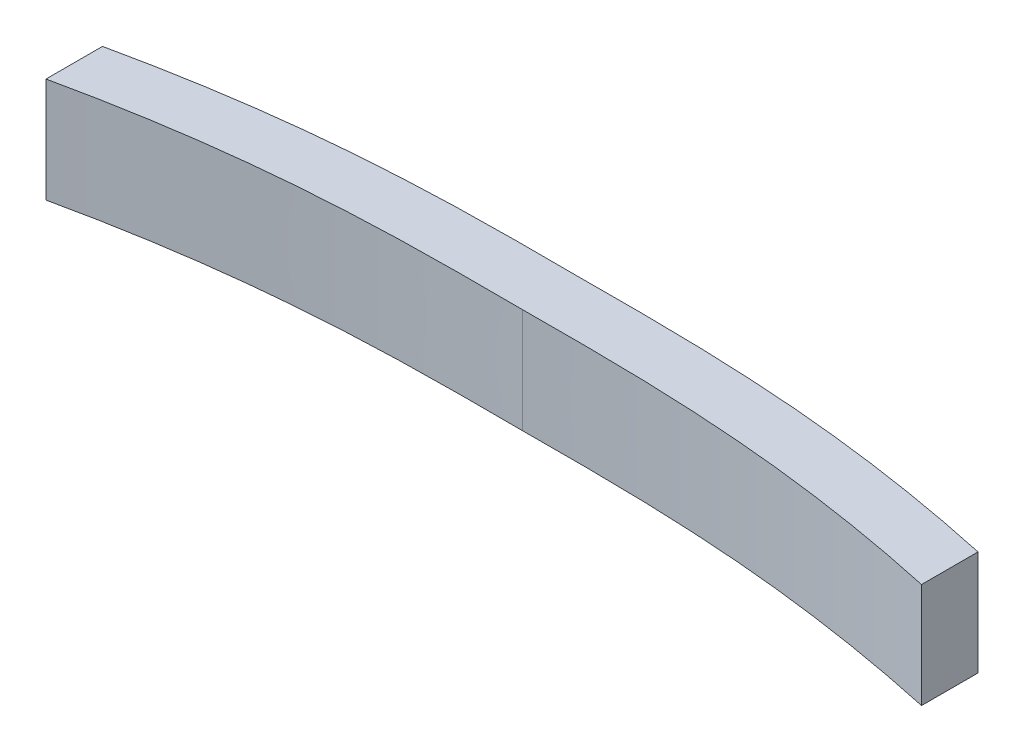
SolidWorks part; units mm, degrees
ref_plane "Front Plane" through (0, 0, 0) normal (0, 0, 1) x (1, 0, 0)
ref_plane "Top Plane" through (0, 0, 0) normal (0, 1, 0) x (1, 0, 0)
ref_plane "Right Plane" through (0, 0, 0) normal (1, 0, 0) x (0, 0, -1)
sketch "Sketch1" plane through (0, 0, 0) normal (0, 1, 0) x (1, 0, 0)
  line L0 (189.6667, 320) -> (948.3333, 320) construction
  line L1 (-903.6669, 221.9416) -> (-806.6741, 223.1267) construction
  line L2 (-2.4415, 6.8053) -> (-2.4415, 30.0052) construction
  line L3 (-115.408, 6.8053) -> (110.5249, 6.8053)
  line L4 (-115.408, 6.8053) -> (-115.408, -50.1579)
  line L5 (-115.408, -50.1579) -> (110.5249, -50.1579)
  line L6 (110.5249, 6.8053) -> (110.5249, -50.1579)
  line L7 (-2.4415, 6.8053) -> (-2.4415, -2.9496) construction
  line L8 (-56.7109, 8.0428) -> (-56.7109, -1.9572)
  line L9 (51.8279, 8.0428) -> (51.8279, -1.9572)
  line L10 (-56.7109, 10.0428) -> (-56.7109, -3.9572)
  line L11 (51.8279, -3.9572) -> (51.8279, 10.0428)
  spline S0 degree 3 poles (-56.7109, 8.0428) (-48.3237, 9.8705) (-35.0274, 11.9379) (-16.8793, 12.8603) (-7.6058, 12.8449) (-2.4415, 12.8177) knots 0 0 0 0 0.472031 0.735861 1 1 1 1
  spline S1 degree 3 poles (-56.7109, -1.9572) (-48.3237, -0.1295) (-35.0274, 1.9379) (-16.8793, 2.8603) (-7.6058, 2.8449) (-2.4415, 2.8177) knots 0 0 0 0 0.472031 0.735861 1 1 1 1
  spline S2 degree 3 poles (51.8279, -1.9572) (43.4407, -0.1295) (30.1443, 1.9379) (11.9963, 2.8603) (2.7228, 2.8449) (-2.4415, 2.8177) knots 0 0 0 0 0.472031 0.735861 1 1 1 1
  spline S3 degree 3 poles (51.8279, 8.0428) (43.4407, 9.8705) (30.1443, 11.9379) (11.9963, 12.8603) (2.7228, 12.8449) (-2.4415, 12.8177) knots 0 0 0 0 0.472031 0.735861 1 1 1 1
  spline S4 degree 3 poles (-56.7109, 10.0428) (-48.3237, 11.8705) (-35.0274, 13.9379) (-16.8793, 14.8603) (-7.6058, 14.8449) (-2.4415, 14.8177) knots 0 0 0 0 0.472031 0.735861 1 1 1 1
  spline S5 degree 3 poles (51.8279, 10.0428) (43.4407, 11.8705) (30.1443, 13.9379) (11.9963, 14.8603) (2.7228, 14.8449) (-2.4415, 14.8177) knots 0 0 0 0 0.472031 0.735861 1 1 1 1
  spline S6 degree 3 poles (-56.7109, -3.9572) (-48.3237, -2.1295) (-35.0274, -0.0621) (-16.8793, 0.8603) (-7.6058, 0.8449) (-2.4415, 0.8177) knots 0 0 0 0 0.472031 0.735861 1 1 1 1
  spline S7 degree 3 poles (51.8279, -3.9572) (43.4407, -2.1295) (30.1443, -0.0621) (11.9963, 0.8603) (2.7228, 0.8449) (-2.4415, 0.8177) knots 0 0 0 0 0.472031 0.735861 1 1 1 1
  spline S8 degree 3 poles (-56.7109, 3.0428) (-48.3237, 4.8705) (-35.0274, 6.9379) (-16.8793, 7.8603) (-7.6058, 7.8449) (-2.4415, 7.8177) knots 0 0 0 0 0.472031 0.735861 1 1 1 1
  spline S9 degree 3 poles (51.8279, 3.0428) (43.4407, 4.8705) (30.1443, 6.9379) (11.9963, 7.8603) (2.7228, 7.8449) (-2.4415, 7.8177) knots 0 0 0 0 0.472031 0.735861 1 1 1 1
  point P30 (-56.7109, 3.0428)
  dimension "D2" = 7
  dimension "D1" = 97
extrude "Boss-Extrude1" add sketch "Sketch1" along normal blind 14 contours L11 S5 S4 L10 S0 S3 | S9 L3 L9 S3 S0 L8 S8 | L8 S8 L3 | S9 L9 L3
sketch "Sketch2" plane through (0, 14, 0) normal (0, 1, 0) x (1, 0, 0)
  line L0 (-55.7109, 4.2581) -> (-55.7109, 16.468)
  line L1 (-56.7109, 10.0428) -> (-56.7109, 3.0428) construction
  line L2 (-2.4415, 14.8177) -> (-2.4415, 22.16) construction
  line L3 (50.8279, 4.2581) -> (50.8279, 19.3538)
  line L4 (51.8279, 3.0428) -> (51.8279, 10.0428) construction
  line L5 (-55.7109, 16.468) -> (50.8279, 19.3538)
  spline S0 degree 3 poles (-56.7109, 4.0428) (-51.0153, 5.2834) (-42.2215, 6.8261) (-30.4783, 8.0862) (-21.9608, 8.606) (-12.6803, 8.8661) (-2.4883, 8.7888) (7.8396, 8.8667) (17.1432, 8.6046) (25.5947, 8.0817) (37.2496, 6.8392) (46.0225, 5.3073) (51.8279, 4.0428) knots 0 0 0 0 0.160114 0.245012 0.324303 0.394459 0.5 0.604256 0.678146 0.755619 0.836799 1 1 1 1
  point P0 (0, 0)
  dimension "D1" = 1
  dimension "D2" = 1
extrude "Cut-Extrude1" cut sketch "Sketch2" against normal blind 12 from offset 1 offset against normal yes
sketch "Sketch4" plane through (0, 14, 0) normal (0, 1, 0) x (1, 0, 0)
  spline S0 degree 3 poles (-56.7109, 10.0428) (-50.8701, 11.3153) (-42.2893, 12.8107) (-30.7314, 14.0577) (-22.3353, 14.5939) (-12.8364, 14.8675) (-2.5876, 14.7894) (7.6773, 14.8667) (17.0747, 14.6115) (25.6741, 14.0764) (37.362, 12.8198) (46.0425, 11.3031) (51.8279, 10.0428) knots 0 0 0 0 0.1642 0.239012 0.319235 0.395239 0.5 0.600749 0.677198 0.758187 0.837359 1 1 1 1
  spline S1 degree 3 poles (-56.7109, 10.0428) (-48.3237, 11.8705) (-35.0274, 13.9379) (-16.8793, 14.8603) (-7.6058, 14.8449) (-2.4415, 14.8177) knots 0 0 0 0 0.472031 0.735861 1 1 1 1 construction
  spline S2 degree 3 poles (51.8279, 10.0428) (43.4407, 11.8705) (30.1443, 13.9379) (11.9963, 14.8603) (2.7228, 14.8449) (-2.4415, 14.8177) knots 0 0 0 0 0.472031 0.735861 1 1 1 1 construction
sketch "Sketch5" plane through (0, 1, 0) normal (0, 1, 0) x (1, 0, 0)
  circle A0 centre (-2.4415, 14.8177) radius 2
  dimension "D1" = 0
  dimension "D2" = 0
  dimension "D3" = 4
extrude "Cut-Extrude2" cut sketch "Sketch5" against normal blind 10
sketch "Sketch6" plane through (0, 0, 0) normal (0, 0, 1) x (1, 0, 0)
  line L0 (49.8279, 1) -> (-54.7109, 1) construction
  line L1 (-59.3897, 1) -> (57.9294, 1)
  line L2 (-59.3897, 1) -> (-59.3897, -9.7624)
  line L3 (-59.3897, -9.7624) -> (57.9294, -9.7624)
  line L4 (57.9294, 1) -> (57.9294, -9.7624)
  dimension "D1" = 0
extrude "Cut-Extrude3" cut sketch "Sketch6" against normal through all both and the other way through all
